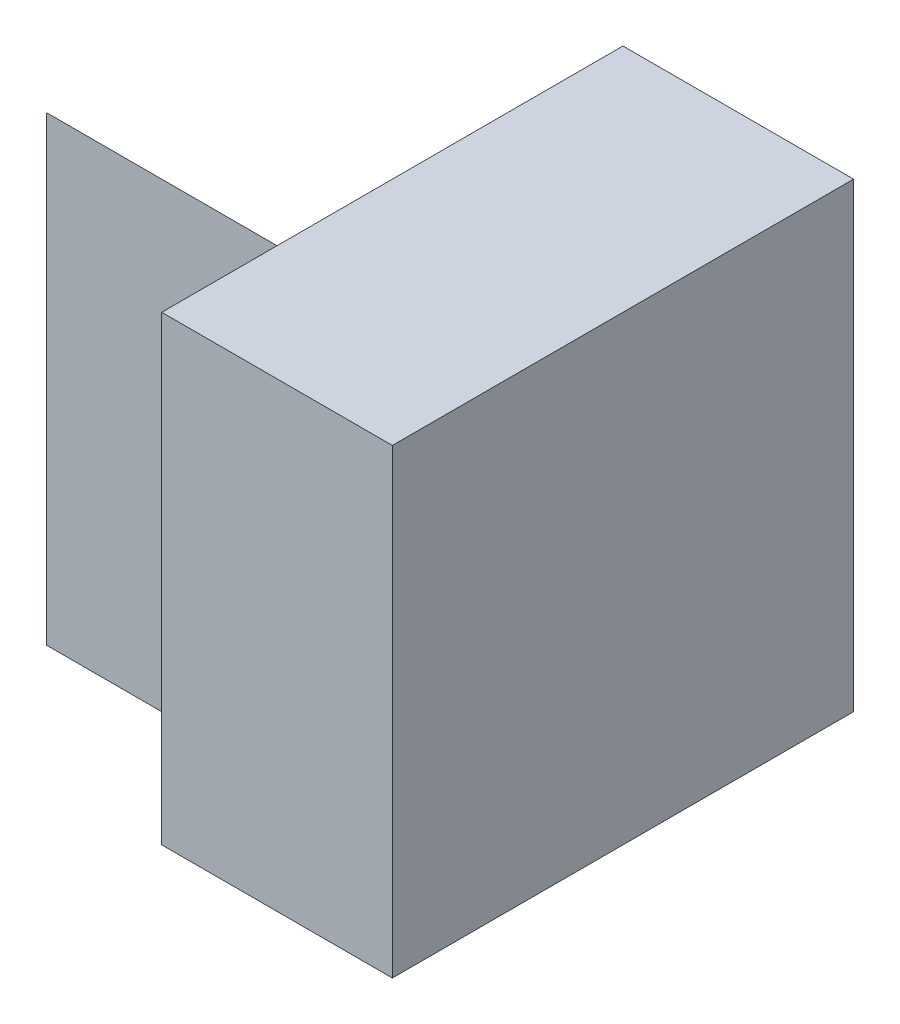
SolidWorks part; units mm, degrees
ref_plane "Front Plane" through (0, 0, 0) normal (0, 0, 1) x (1, 0, 0)
ref_plane "Top Plane" through (0, 0, 0) normal (0, 1, 0) x (1, 0, 0)
ref_plane "Right Plane" through (0, 0, 0) normal (1, 0, 0) x (0, 0, -1)
sketch "Sketch1" plane through (0, 0, 0) normal (1, 0, 0) x (0, 0, -1)
  line L1 (0, 0) -> (4, 0)
  line L2 (0, 0) -> (0, 4)
  line L3 (0, 4) -> (4, 4)
  line L4 (4, 0) -> (4, 4)
  dimension "D1" = 4
  dimension "D2" = 4
extrude "Boss-Extrude1" add sketch "Sketch1" along normal blind 2
sketch "Sketch2" plane through (0, 0, 0) normal (-1, 0, 0) x (0, 0, 1)
  line L0 (-1, 0) -> (-1, 4)
  line L1 (0, 0) -> (-4, 0) construction
  line L2 (-4, 0) -> (-4, 4) construction
  line L3 (-4, 4) -> (-4, 0)
  line L4 (-4, 0) -> (-1, 0)
  line L5 (-4, 4) -> (0, 4) construction
  line L6 (-1, 4) -> (-4, 4)
  dimension "D1" = 3
  dimension "D2" = 4
extrude "Boss-Extrude2" add sketch "Sketch2" along normal blind 2
sketch "Sketch3" plane through (-2, 0, 0) normal (-1, 0, 0) x (0, 0, 1)
  line L0 (-1, 4) -> (-4, 0)
  line L1 (-4, 0) -> (-4, 4)
  line L2 (-4, 4) -> (-1, 4)
extrude "Cut-Extrude1" cut sketch "Sketch3" against normal blind 2
